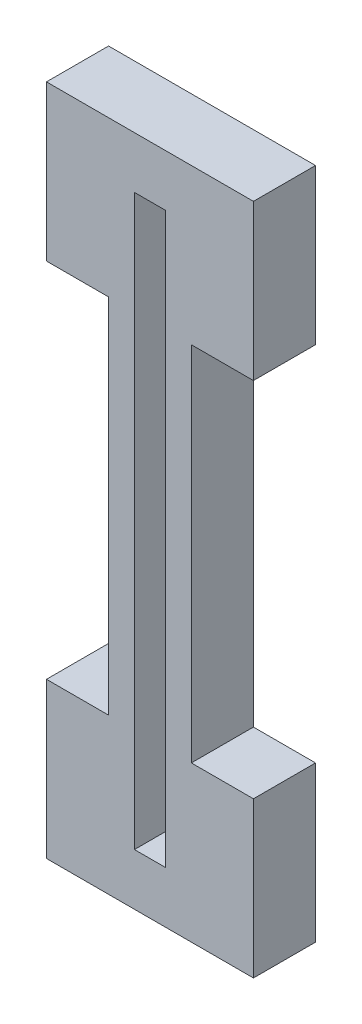
SolidWorks part; units mm, degrees
ref_plane "Front Plane" through (0, 0, 0) normal (0, 0, 1) x (1, 0, 0)
ref_plane "Top Plane" through (0, 0, 0) normal (0, 1, 0) x (1, 0, 0)
ref_plane "Right Plane" through (0, 0, 0) normal (1, 0, 0) x (0, 0, -1)
sketch "Sketch1" plane through (0, 0, 0) normal (0, 0, 1) x (1, 0, 0)
  line L0 (10, 65) -> (10, 14.7849) construction
  line L1 (0, 0) -> (20, 0)
  line L2 (0, 0) -> (0, 15)
  line L3 (0, 65) -> (20, 65)
  line L4 (20, 0) -> (20, 15)
  line L5 (0, 50) -> (6, 50)
  line L7 (0, 15) -> (6, 15)
  line L8 (6, 50) -> (6, 15)
  line L9 (20, 15) -> (14, 15)
  line L10 (14, 50) -> (14, 15)
  line L11 (20, 50) -> (14, 50)
  line L13 (0, 50) -> (0, 65)
  line L14 (20, 50) -> (20, 65)
  line L16 (8.5, 60) -> (11.5, 60)
  line L17 (8.5, 60) -> (8.5, 5)
  line L18 (8.5, 5) -> (11.5, 5)
  line L19 (11.5, 60) -> (11.5, 5)
  point P19 (10, 5)
  point P20 (0, 0)
  dimension "D1" = 6
  dimension "D2" = 35
  dimension "D3" = 15
  dimension "D4" = 15
  dimension "D5" = 8
  dimension "D6" = 5
  dimension "D7" = 5
  dimension "D8" = 3
extrude "Boss-Extrude1" add sketch "Sketch1" along normal blind 6
